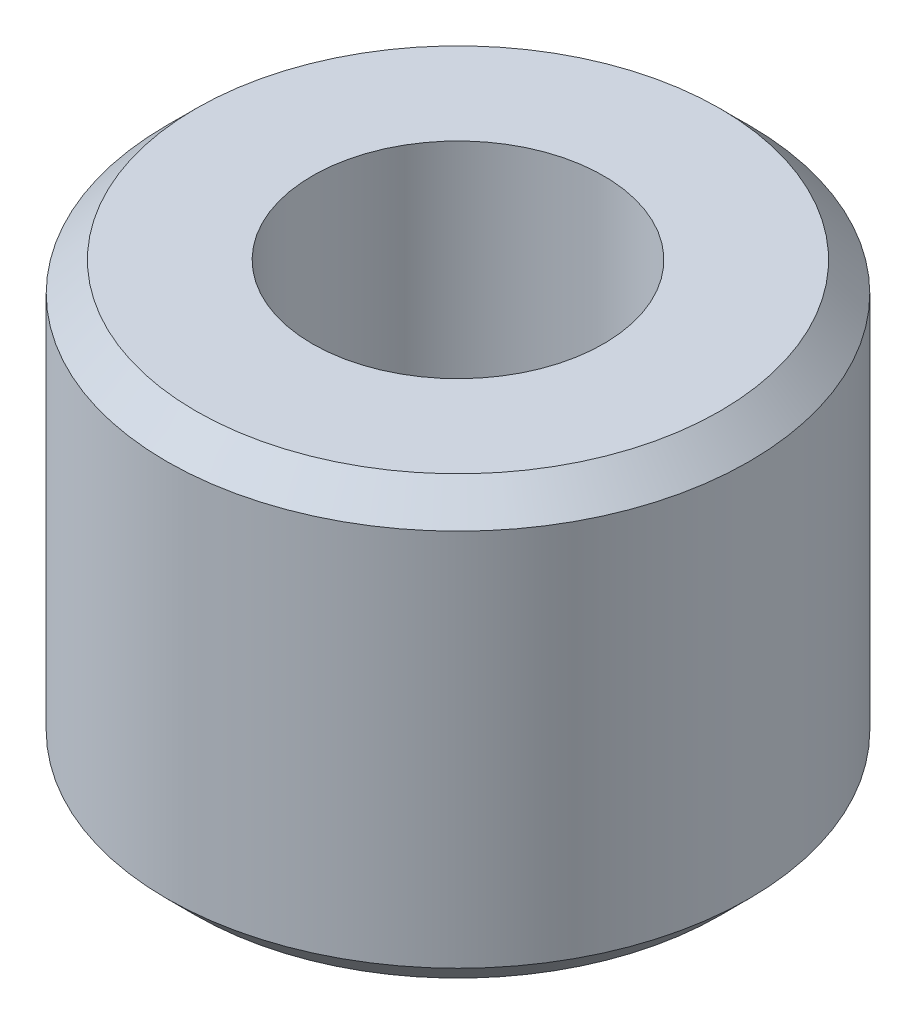
SolidWorks part; units mm, degrees
ref_plane "Front Plane" through (0, 0, 0) normal (0, 0, 1) x (1, 0, 0)
ref_plane "Top Plane" through (0, 0, 0) normal (0, 1, 0) x (1, 0, 0)
ref_plane "Right Plane" through (0, 0, 0) normal (1, 0, 0) x (0, 0, -1)
sketch "Sketch1" plane through (0, 0, 0) normal (0, 1, 0) x (1, 0, 0)
  circle A0 centre (0, 0) radius 10
extrude "Boss-Extrude1" add sketch "Sketch1" along normal blind 15
sketch "Sketch2" plane through (0, 15, 0) normal (0, 1, 0) x (1, 0, 0)
  circle A0 centre (0, 0) radius 5
extrude "Cut-Extrude1" cut sketch "Sketch2" against normal blind 15
chamfer "Chamfer1" distance 1 angle 45 2 edges at (0, 0, 10) (0, 15, 10)
